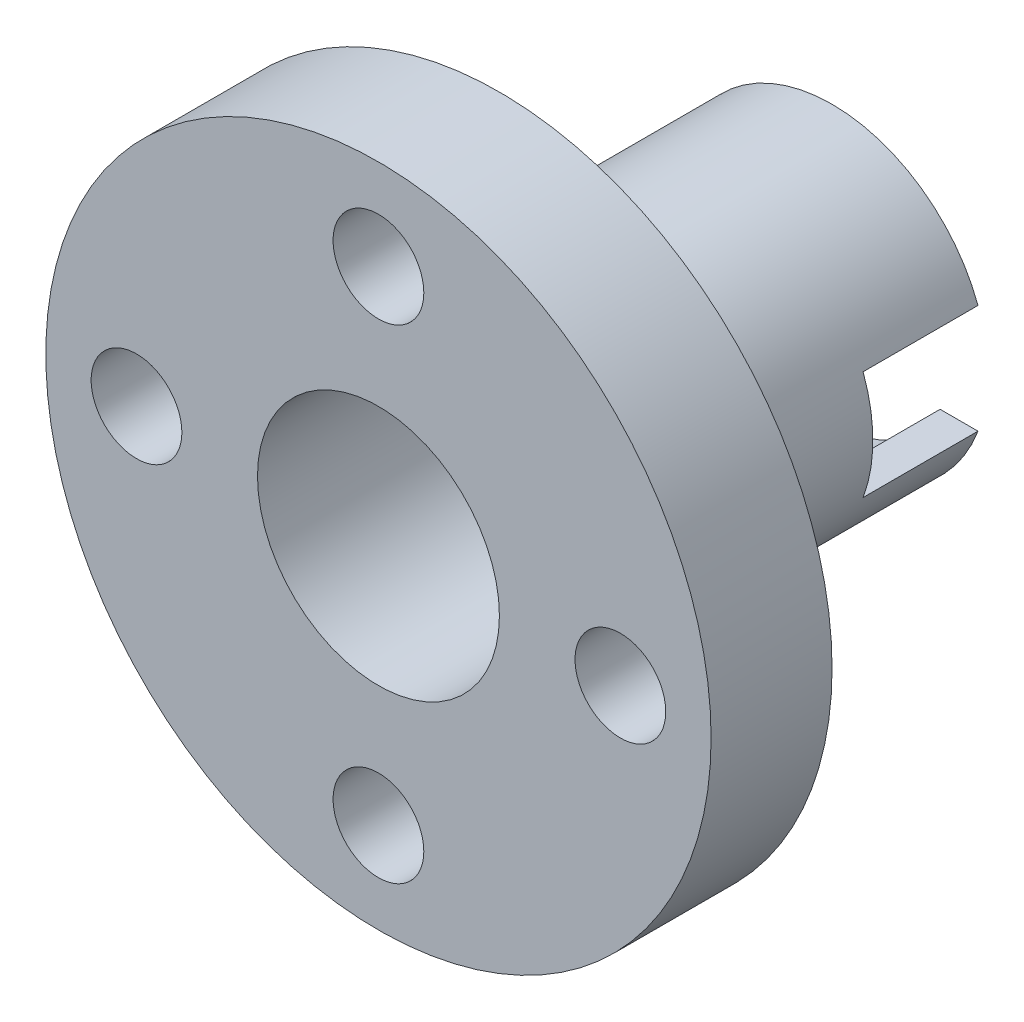
SolidWorks part; units mm, degrees
ref_plane "前视基准面" through (0, 0, 0) normal (0, 0, 1) x (1, 0, 0)
ref_plane "上视基准面" through (0, 0, 0) normal (0, 1, 0) x (1, 0, 0)
ref_plane "右视基准面" through (0, 0, 0) normal (1, 0, 0) x (0, 0, -1)
sketch "草图1" plane through (0, 0, 0) normal (0, 0, 1) x (1, 0, 0)
  line L0 (-11, 0) -> (11, 0) construction
  line L1 (0, 11) -> (0, -11) construction
  circle A0 centre (0, 0) radius 11
  circle A1 centre (-8, 0) radius 1.5
  circle A2 centre (0, 8) radius 1.5
  circle A3 centre (8, 0) radius 1.5
  circle A4 centre (0, -8) radius 1.5
  point P18 (0, 0)
  dimension "D1" = 22
  dimension "D2" = 3
  dimension "D3" = 8
  dimension "D4" = 4
extrude "凸台-拉伸1" add sketch "草图1" along normal blind 4
sketch "草图2" plane through (0, 0, 0) normal (0, 0, -1) x (-1, 0, 0)
  circle A0 centre (0, 0) radius 5.15
  dimension "D1" = 10.3
extrude "凸台-拉伸2" add sketch "草图2" along normal blind 11
sketch "草图3" plane through (0, 0, -11) normal (0, 0, -1) x (-1, 0, 0)
  circle A0 centre (0, 0) radius 4
  dimension "D1" = 8
extrude "切除-拉伸1" cut sketch "草图3" against normal through all both and the other way through all
sketch "草图4" plane through (0, 0, 0) normal (0, 0, -1) x (-1, 0, 0)
  circle A0 centre (0, 8) radius 1.5 construction
  circle A1 centre (0, -8) radius 1.5 construction
  point P0 (0, 6.5)
  point P1 (0, -6.5)
sketch "草图5" plane through (0, 0, 4) normal (0, 0, 1) x (1, 0, 0)
  circle A0 centre (0, 8) radius 1.5 construction
  point P0 (0, 6.5)
ref_plane "基准面1" through (0, 0, 0) normal (-1, 0, 0) x (0, 0, 1)
sketch "草图6" plane through (0, 0, 0) normal (-1, 0, 0) x (0, 0, 1)
  line L1 (-11, 4.8906) -> (-11, 6.0406) construction
  line L3 (-11, 1.8) -> (-7.2, 1.8)
  line L4 (-11, 1.8) -> (-11, -1.8)
  line L5 (-11, -1.8) -> (-7.2, -1.8)
  line L6 (-7.2, 1.8) -> (-7.2, -1.8)
  dimension "D1" = 3.8
  dimension "D2" = 3.6
  dimension "D3" = 7.2
  dimension "D4" = 1.8
extrude "切除-拉伸2" cut sketch "草图6" against normal through all both and the other way through all
